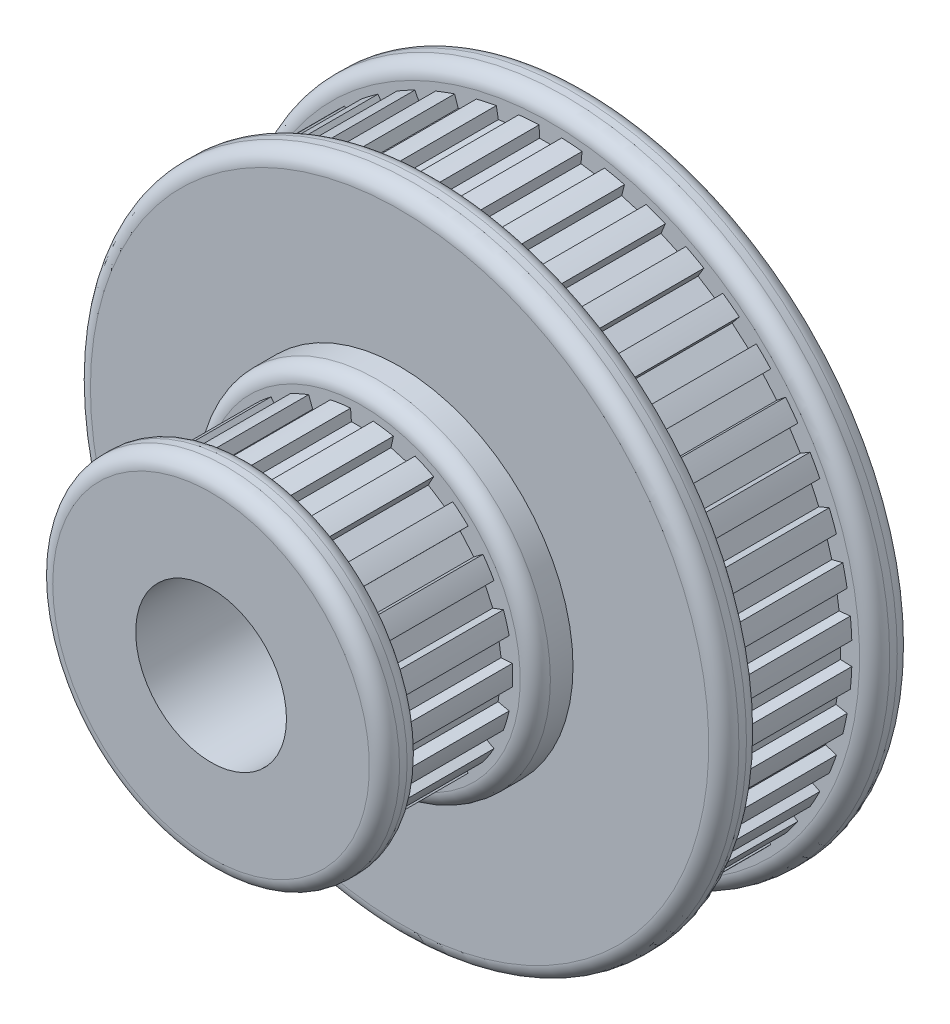
SolidWorks part; units mm, degrees
ref_plane "Front Plane" through (0, 0, 0) normal (0, 0, 1) x (1, 0, 0)
ref_plane "Top Plane" through (0, 0, 0) normal (0, 1, 0) x (1, 0, 0)
ref_plane "Right Plane" through (0, 0, 0) normal (1, 0, 0) x (0, 0, -1)
sketch "Sketch1" plane through (0, 0, 0) normal (1, 0, 0) x (0, 0, -1)
  line L0 (0, 0) -> (32.3469, 0) construction
  line L1 (0, 10) -> (50, 10)
  line L2 (50, 10) -> (50, 43)
  line L3 (50, 43) -> (45, 43)
  line L4 (45, 43) -> (45, 40)
  line L5 (45, 40) -> (30, 40)
  line L6 (30, 40) -> (30, 43)
  line L7 (30, 43) -> (25, 43)
  line L8 (25, 43) -> (25, 23)
  line L9 (25, 23) -> (20, 23)
  line L10 (20, 23) -> (20, 20)
  line L11 (20, 20) -> (5, 20)
  line L12 (5, 20) -> (5, 23)
  line L13 (5, 23) -> (0, 23)
  line L14 (0, 23) -> (0, 10)
  dimension "D1" = 5
  dimension "D2" = 15
  dimension "D3" = 15
  dimension "D4" = 43
  dimension "D5" = 23
  dimension "D6" = 5
  dimension "D7" = 5
  dimension "D8" = 5
  dimension "D9" = 3
  dimension "D10" = 3
  dimension "D11" = 10
revolve "Revolve1" add sketch "Sketch1" angle 360 about L0
sketch "Sketch2" plane through (0, 0, -20) normal (0, 0, 1) x (1, 0, 0)
  line L0 (-1.3872, 18.4437) -> (1.3872, 18.4437)
  line L1 (1.3872, 18.4437) -> (1.5, 19.9437)
  line L2 (-1.3872, 18.4437) -> (-1.5, 19.9437)
  circle A0 centre (0, 0) radius 20 construction
  arc A1 (1.5, 19.9437) -> (-1.5, 19.9437) centre (0, 0) ccw
  point P5 (0, 18.4437)
  dimension "D1" = 1.5
  dimension "D2" = 3
extrude "Cut-Extrude1" cut sketch "Sketch2" along normal up to surface (15 mm away) up to face at (23, 0, -5)
pattern_circular "CirPattern1" count 22 over 360 about axis through (0, 0, 0) along (0, 0, 1) of "Cut-Extrude1"
sketch "Sketch3" plane through (0, 0, -45) normal (0, 0, 1) x (1, 0, 0)
  line L0 (-1.4437, 38.4719) -> (1.4437, 38.4719)
  line L1 (1.4437, 38.4719) -> (1.5, 39.9719)
  line L2 (-1.4437, 38.4719) -> (-1.5, 39.9719)
  circle A0 centre (0, 0) radius 40 construction
  arc A1 (1.5, 39.9719) -> (-1.5, 39.9719) centre (0, 0) ccw
  point P5 (0, 38.4719)
  dimension "D1" = 1.5
  dimension "D2" = 3
extrude "Cut-Extrude2" cut sketch "Sketch3" along normal up to surface (15 mm away) up to face at (43, 0, -30)
pattern_circular "CirPattern2" count 44 over 360 about axis through (0, 0, 0) along (0, 0, 1) of "Cut-Extrude2"
sketch "Sketch5" plane through (0, 0, 0) normal (1, 0, 0) x (0, 0, -1)
  line L0 (50, 35.5) -> (50, 21)
  line L1 (50, -43) -> (50, 43) construction
  line L2 (50, 21) -> (40, 26.7735)
  line L3 (40, 26.7735) -> (40, 29.7265)
  line L4 (40, 29.7265) -> (50, 35.5)
  line L5 (0, 0) -> (58.9546, 0) construction
  dimension "D1" = 10
  dimension "D2" = 7.5
  dimension "D3" = 60
  dimension "D4" = 14.5
revolve "Cut-Revolve4" cut sketch "Sketch5" angle 360 about L5
fillet "Fillet1" radius 2 7 edges at (23, 0, 0) (23, 0, -5) (23, 0, -20) (43, 0, -25) (43, 0, -30) (43, 0, -45) (43, 0, -50)
fillet "Fillet2" radius 2 4 edges at (21, 0, -50) (26.7735, 0, -40) (29.7265, 0, -40) (35.5, 0, -50)
